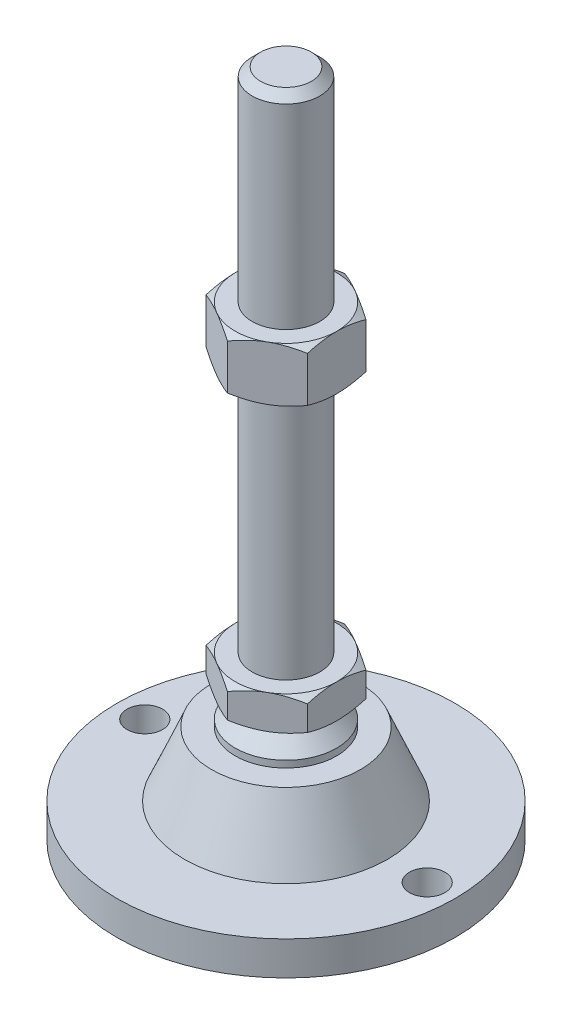
SolidWorks part; units mm, degrees
ref_plane "Спереди" through (0, 0, 0) normal (0, 0, 1) x (1, 0, 0)
ref_plane "Сверху" through (0, 0, 0) normal (0, 1, 0) x (1, 0, 0)
ref_plane "Справа" through (0, 0, 0) normal (1, 0, 0) x (0, 0, -1)
sketch "Эскиз1" plane through (0, 0, 0) normal (0, 0, 1) x (1, 0, 0)
  line L0 (0, 0) -> (-50, 0)
  line L3 (-50, 0) -> (-50, 10)
  line L12 (-10, 48) -> (-10, 195.5)
  line L13 (-10, 195.5) -> (-7.5, 198)
  line L14 (-7.5, 198) -> (0, 198)
  line L15 (0, 198) -> (0, 0) construction
  line L16 (-50, 10) -> (-30, 10)
  line L17 (0, 0) -> (0, 198)
  line L18 (0, 0) -> (0, -7.9595) construction
  line L19 (-10, 48) -> (-10, 38)
  line L21 (-15, 29) -> (-22, 29)
  line L22 (-30, 10) -> (-22, 29)
  line L23 (-15, 29) -> (-15, 31)
  line L24 (-15, 31) -> (-10, 36)
  line L25 (-10, 36) -> (-10, 38)
  line L26 (-10, 48) -> (0, 48) construction
  point P8 (-10, 121.75)
revolve "Повернуть1" add sketch "Эскиз1" angle 360 about L17
ref_plane "Плоскость2" through (0, 38, 0) normal (0, 1, 0) x (1, 0, 0)
sketch "Эскиз2" plane through (0, 38, 0) normal (0, 1, 0) x (1, 0, 0)
  line L1 (0, 17.3205) -> (-15, 8.6603)
  line L2 (-15, 8.6603) -> (-15, -8.6603)
  line L3 (-15, -8.6603) -> (0, -17.3205)
  line L4 (0, -17.3205) -> (15, -8.6603)
  line L5 (15, -8.6603) -> (15, 8.6603)
  line L6 (15, 8.6603) -> (0, 17.3205)
  circle A0 centre (0, 0) radius 15 construction
  dimension "D1" = 30
extrude "Бобышка-Вытянуть1" add sketch "Эскиз2" along normal up to vertex (10 mm away) up to point (-10, 48, 0)
ref_plane "Плоскость1" through (0, 121.75, 0) normal (0, 1, 0) x (1, 0, 0)
sketch "Эскиз3" plane through (0, 121.75, 0) normal (0, 1, 0) x (1, 0, 0)
  line L6 (15, 8.6603) -> (0, 17.3205)
  line L7 (0, 17.3205) -> (-15, 8.6603)
  line L8 (-15, 8.6603) -> (-15, -8.6603)
  line L9 (-15, -8.6603) -> (0, -17.3205)
  line L10 (0, -17.3205) -> (15, -8.6603)
  line L11 (15, -8.6603) -> (15, 8.6603)
  line L12 (15, 8.6603) -> (0, 17.3205)
  line L13 (0, 17.3205) -> (-15, 8.6603)
  line L14 (-15, 8.6603) -> (-15, -8.6603)
  line L15 (-15, -8.6603) -> (0, -17.3205)
  line L16 (0, -17.3205) -> (15, -8.6603)
  line L17 (15, -8.6603) -> (15, 8.6603)
  dimension "D1" = 0
extrude "Бобышка-Вытянуть2" add sketch "Эскиз3" along normal blind 16
sketch "Эскиз4" plane through (0, 0, 0) normal (0, 0, 1) x (1, 0, 0)
  line L0 (-15, 137.75) -> (-28.8564, 129.75)
  line L1 (-28.8564, 129.75) -> (-28.8564, 137.75)
  line L2 (-28.8564, 137.75) -> (-15, 137.75)
  line L3 (-28.8564, 129.75) -> (-15, 121.75)
  line L4 (50, 121.75) -> (-50, 121.75) construction
  line L5 (-15, 121.75) -> (-28.8564, 121.75)
  line L6 (-28.8564, 121.75) -> (-28.8564, 129.75)
  line L7 (-15, 137.75) -> (-15, 121.75) construction
  line L8 (-15, 48) -> (-23.6603, 48)
  line L9 (-23.6603, 48) -> (-23.6603, 43)
  line L10 (-23.6603, 43) -> (-15, 48)
  line L11 (-15, 38) -> (-23.6603, 43)
  line L12 (-23.6603, 43) -> (-23.6603, 38)
  line L13 (-23.6603, 38) -> (-15, 38)
  line L14 (0, 198) -> (0, 96.3793) construction
  line L15 (50, 38) -> (-50, 38) construction
  dimension "D1" = 30
  dimension "D2" = 30
revolve "Вырез-Повернуть2" cut sketch "Эскиз4" angle 360 about L14
sketch "Эскиз5" plane through (0, 10, 0) normal (0, 1, 0) x (1, 0, 0)
  line L0 (41.75, 0) -> (-41.75, 0) construction
  circle A0 centre (-41.75, 0) radius 5.25
  circle A1 centre (41.75, 0) radius 5.25
  circle A2 centre (0, 0) radius 50 construction
  dimension "D1" = 10.5
  dimension "D2" = 3
extrude "Вырез-Вытянуть1" cut sketch "Эскиз5" against normal through all
equation "\"D13@Эскиз1\"=\"D12@Эскиз1\"/2"
